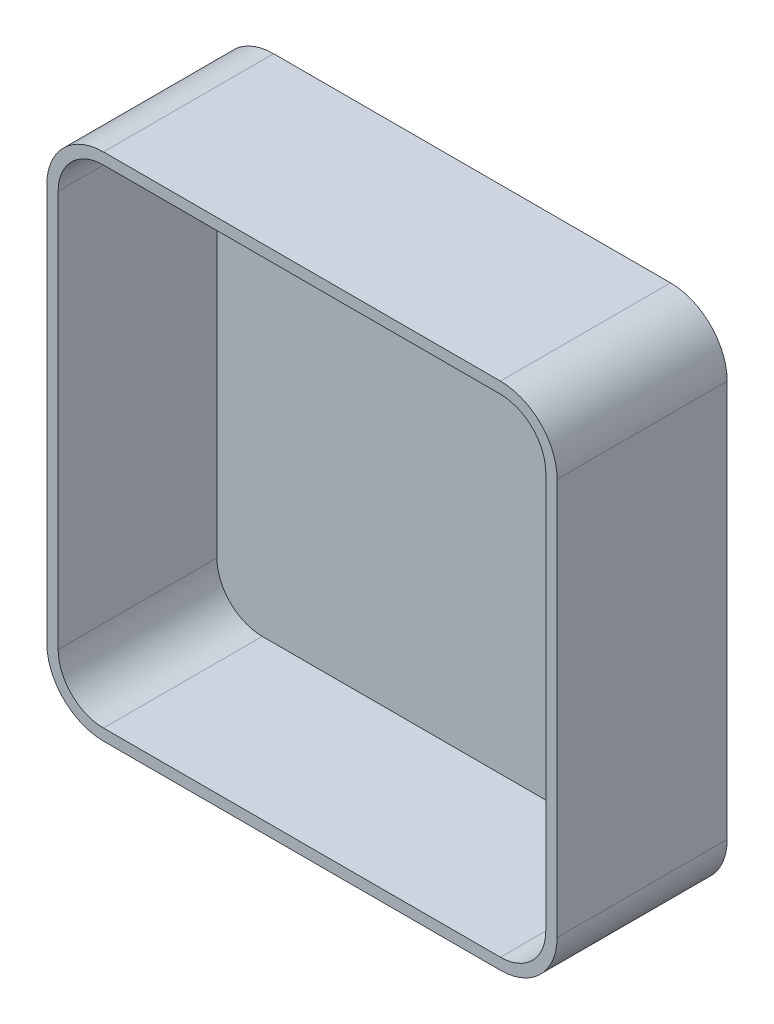
SolidWorks part; units mm, degrees
ref_plane "前视基准面" through (0, 0, 0) normal (0, 0, 1) x (1, 0, 0)
ref_plane "上视基准面" through (0, 0, 0) normal (0, 1, 0) x (1, 0, 0)
ref_plane "右视基准面" through (0, 0, 0) normal (1, 0, 0) x (0, 0, -1)
sketch "Sketch1" plane through (0, 0, 0) normal (0, 0, 1) x (1, 0, 0)
  line L1 (0, 0) -> (45, 0)
  line L2 (0, 0) -> (0, 45)
  line L3 (0, 45) -> (45, 45)
  line L4 (45, 0) -> (45, 45)
  dimension "D1" = 45
  dimension "D2" = 45
extrude "Boss-Extrude1" add sketch "Sketch1" along normal blind 15
fillet "Fillet1" radius 5 4 edges at (0, 0, 7.5) (45, 0, 7.5) (45, 45, 7.5) (0, 45, 7.5)
shell "Shell1" thickness 1
